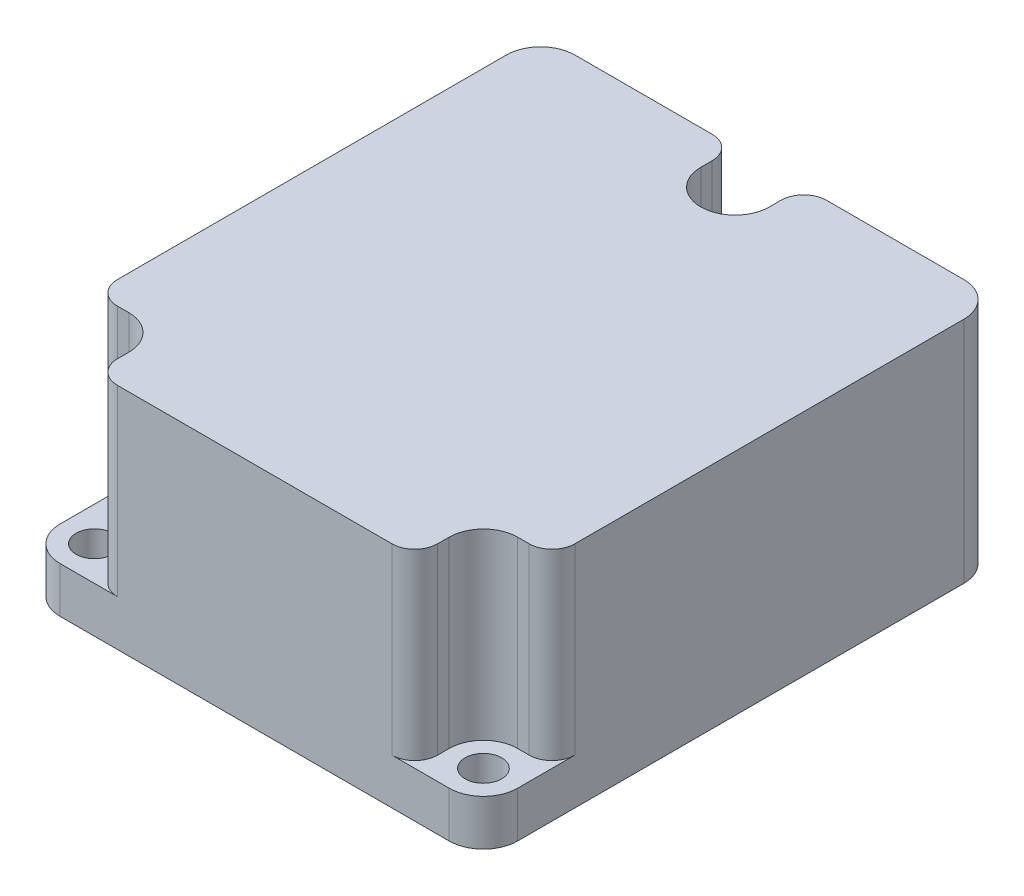
SolidWorks part; units mm, degrees
material "6061 合金"
ref_plane "前视基准面" through (0, 0, 0) normal (0, 0, 1) x (1, 0, 0)
ref_plane "上视基准面" through (0, 0, 0) normal (0, 1, 0) x (1, 0, 0)
ref_plane "右视基准面" through (0, 0, 0) normal (1, 0, 0) x (0, 0, -1)
sketch "草图1" plane through (0, 0, 0) normal (0, 1, 0) x (1, 0, 0)
  line L0 (20, 0) -> (20, -45) construction
  line L1 (3, 0) -> (37, 0)
  line L2 (0, -3) -> (0, -42)
  line L3 (3, -45) -> (37, -45)
  line L4 (40, -3) -> (40, -42)
  line L5 (20, 0) -> (20, -3) construction
  line L6 (20, -45) -> (20, -42) construction
  line L7 (3, -42) -> (37, -42) construction
  circle A0 centre (20, -3) radius 1.6
  circle A1 centre (3, -42) radius 1.6
  circle A2 centre (37, -42) radius 1.6
  arc A3 (0, -42) -> (3, -45) centre (3, -42) ccw
  arc A4 (3, 0) -> (0, -3) centre (3, -3) ccw
  arc A5 (37, 0) -> (40, -3) centre (37, -3) cw
  arc A6 (37, -45) -> (40, -42) centre (37, -42) ccw
  point P13 (20, -42)
  point P19 (0, 0)
  dimension "D1" = 3
extrude "凸台-拉伸1" add sketch "草图1" along normal blind 20
sketch "草图2" plane through (0, 20, 0) normal (0, 1, 0) x (1, 0, 0)
  line L0 (17, -3) -> (17, 0)
  line L1 (23, -3) -> (23, 0)
  line L2 (6, -42) -> (6, -45)
  line L3 (3, -39) -> (0, -39)
  line L4 (3, -45) -> (37, -45)
  line L5 (40, -42) -> (40, -3)
  line L6 (37, 0) -> (3, 0)
  line L7 (0, -3) -> (0, -42)
  line L8 (3, -45) -> (37, -45)
  line L9 (40, -42) -> (40, -3)
  line L10 (37, 0) -> (3, 0)
  line L11 (0, -3) -> (0, -42)
  line L12 (34, -42) -> (34, -45)
  line L13 (37, -39) -> (40, -39)
  arc A0 (37, -45) -> (40, -42) centre (37, -42) ccw
  arc A1 (0, -42) -> (3, -45) centre (3, -42) ccw
  arc A2 (17, -3) -> (23, -3) centre (20, -3) ccw
  arc A3 (6, -42) -> (3, -39) centre (3, -42) ccw
  arc A4 (0, -42) -> (3, -45) centre (3, -42) ccw
  arc A5 (37, -45) -> (40, -42) centre (37, -42) ccw
  arc A6 (40, -3) -> (37, 0) centre (37, -3) ccw
  arc A7 (3, 0) -> (0, -3) centre (3, -3) ccw
  arc A8 (0, -42) -> (3, -45) centre (3, -42) ccw
  arc A9 (37, -45) -> (40, -42) centre (37, -42) ccw
  arc A10 (40, -3) -> (37, 0) centre (37, -3) ccw
  arc A11 (3, 0) -> (0, -3) centre (3, -3) ccw
  arc A12 (37, -39) -> (34, -42) centre (37, -42) ccw
  circle M10 centre (3, -42) radius 1.6
  arc M11 (0, -42) -> (3, -45) centre (3, -42) ccw
  line M12 (3, -45) -> (37, -45)
  arc M13 (37, -45) -> (40, -42) centre (37, -42) ccw
  line M14 (40, -42) -> (40, -3)
  line M16 (37, 0) -> (3, 0)
  line M18 (0, -3) -> (0, -42)
  circle M19 centre (20, -3) radius 1.6
  circle M20 centre (37, -42) radius 1.6
  dimension "D1" = 0
extrude "切除-拉伸1" cut sketch "草图2" against normal blind 16 contours L13 A12 L12 L8 M13 M14 M20 | L2 A3 L3 M18 M11 M12 M10 | L0 A2 L1 M16 M19
fillet "圆角1" radius 2 6 edges at (34, 12, 45) (40, 12, 39) (17, 12, 0) (23, 12, 0) (6, 12, 45) (0, 12, 39)
sketch "草图3" plane through (0, 0, 45) normal (0, 0, 1) x (1, 0, 0)
  line L0 (20, 20) -> (20, 0) construction
  line L1 (8, 20) -> (32, 20) construction
  line L2 (3, 0) -> (37, 0) construction
  circle A0 centre (20, 10) radius 7
extrude "凸台-拉伸2" add sketch "草图3" along normal blind 50
sketch "草图4" plane through (0, 0, 95) normal (0, 0, 1) x (1, 0, 0)
  circle A1 centre (20, 10) radius 7
  circle A2 centre (20, 10) radius 7
  dimension "D1" = 0
extrude "切除-拉伸2" cut sketch "草图4" against normal blind 50
ref_plane "基准面1" through (0, 0, 22.5) normal (0, 0, 1) x (1, 0, 0)
sketch "草图5" plane through (0, 0, 22.5) normal (0, 0, 1) x (1, 0, 0)
  line L0 (20, 20) -> (20, 0) construction
  line L1 (8, 20) -> (32, 20) construction
  line L2 (3, 0) -> (37, 0) construction
  point P6 (20, 10)
